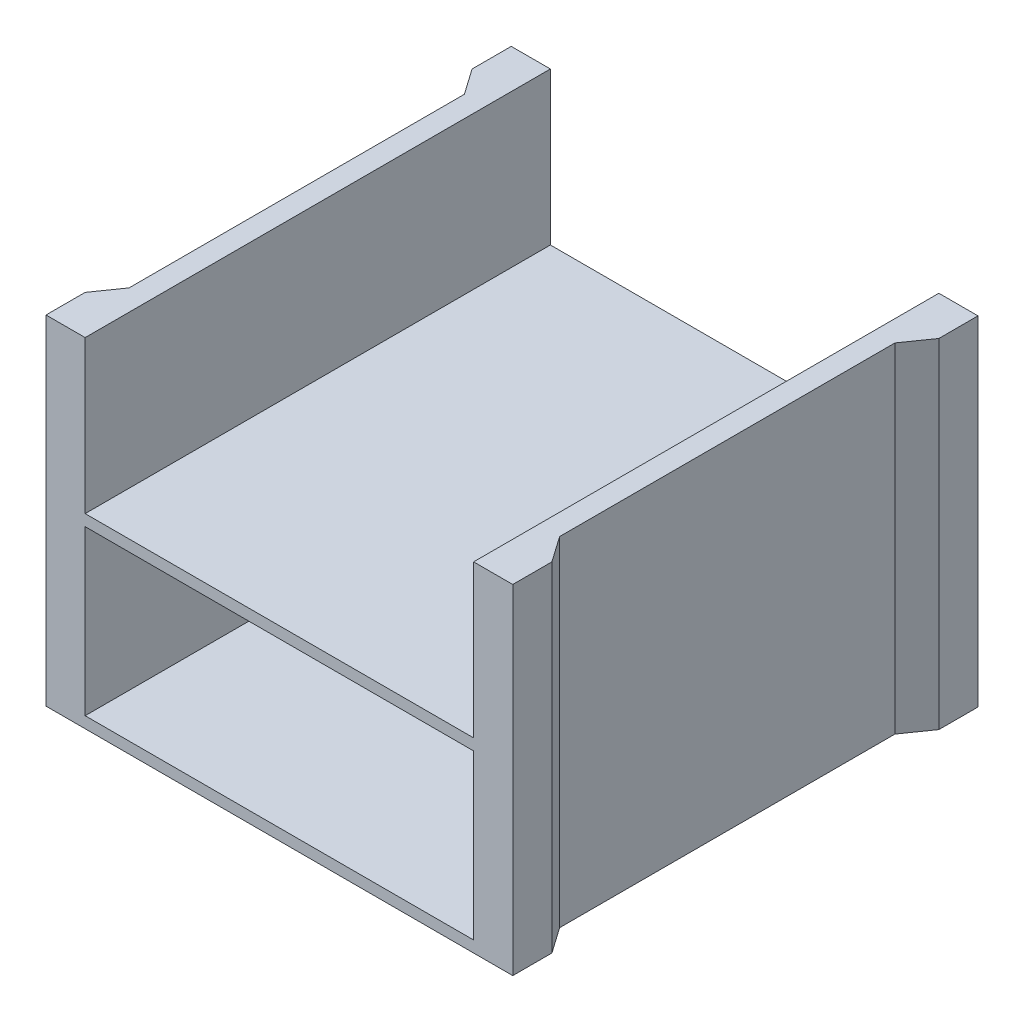
SolidWorks part; units mm, degrees
ref_plane "Front Plane" through (0, 0, 0) normal (0, 0, 1) x (1, 0, 0)
ref_plane "Top Plane" through (0, 0, 0) normal (0, 1, 0) x (1, 0, 0)
ref_plane "Right Plane" through (0, 0, 0) normal (1, 0, 0) x (0, 0, -1)
sketch "Sketch1" plane through (0, 0, 0) normal (0, 1, 0) x (1, 0, 0)
  line L0 (0, 243.586) -> (0, -78.486)
  line L1 (-82.55, -82.55) -> (82.55, -82.55)
  line L2 (-82.55, -82.55) -> (-82.55, 82.55)
  line L3 (-82.55, 82.55) -> (82.55, 82.55)
  line L4 (82.55, -82.55) -> (82.55, 82.55)
  line L5 (-82.55, -82.55) -> (82.55, 82.55) construction
  line L6 (-82.55, 82.55) -> (82.55, -82.55) construction
  line L7 (72.644, 78.486) -> (-72.644, 78.486)
  line L8 (72.644, 78.486) -> (72.644, -78.486)
  line L9 (72.644, -78.486) -> (-72.644, -78.486)
  line L10 (-72.644, 78.486) -> (-72.644, -78.486)
  line L11 (-72.644, 78.486) -> (-78.74, 78.486)
  line L12 (-72.644, 78.486) -> (-72.644, 65.278)
  line L13 (-72.644, 65.278) -> (-78.74, 65.278)
  line L14 (-78.74, 78.486) -> (-78.74, 65.278)
  line L15 (72.644, 0) -> (-72.644, 0)
  line L16 (72.644, 65.278) -> (78.74, 65.278)
  line L17 (78.74, 78.486) -> (78.74, 65.278)
  line L18 (72.644, 78.486) -> (78.74, 78.486)
  line L19 (72.644, 78.486) -> (72.644, 65.278)
  line L20 (72.644, -78.486) -> (78.74, -78.486)
  line L21 (78.74, -78.486) -> (78.74, -65.278)
  line L22 (72.644, -65.278) -> (78.74, -65.278)
  line L23 (72.644, -78.486) -> (72.644, -65.278)
  line L24 (-72.644, -65.278) -> (-78.74, -65.278)
  line L25 (-78.74, -78.486) -> (-78.74, -65.278)
  line L26 (-72.644, -78.486) -> (-78.74, -78.486)
  line L27 (-72.644, -78.486) -> (-72.644, -65.278)
  line L28 (-78.74, 65.278) -> (-72.644, 56.572)
  line L29 (78.74, 65.278) -> (72.644, 56.572)
  line L30 (78.74, -65.278) -> (72.644, -56.572)
  line L31 (-78.74, -65.278) -> (-72.644, -56.572)
  point P0 (0, 0)
  point P26 (0, 82.55)
  dimension "D1" = 165.1
  dimension "D2" = 165.1
  dimension "D3" = 4.064
  dimension "D4" = 4.064
  dimension "D5" = 157.48
  dimension "D6" = 35
  dimension "D7" = 6.096
  dimension "D8" = 13.208
extrude "Boss-Extrude1" add sketch "Sketch1" along normal blind 114.3 contours L15 L8 L7 L0 | L18 L8 L16 L17 | L8 L15 L0 L9 | L0 L15 L10 L9 | L26 L10 L24 L25 | L15 L0 L7 L10 | L12 L13 L14 L11 | L23 L22 L21 L20
sketch "Sketch3" plane through (0, 0, 78.486) normal (0, 0, 1) x (1, 0, 0)
  line L0 (78.74, 114.3) -> (-78.74, 114.3) construction
  line L1 (-65.532, 3.81) -> (65.532, 3.81)
  line L2 (-65.532, 3.81) -> (-65.532, 114.3)
  line L3 (-65.532, 114.3) -> (65.532, 114.3)
  line L4 (65.532, 3.81) -> (65.532, 114.3)
  line L5 (-78.74, 114.3) -> (-78.74, 0) construction
  line L6 (78.74, 114.3) -> (78.74, 0) construction
  line L7 (72.644, 0) -> (-72.644, 0) construction
  line L8 (-65.532, 59.055) -> (65.532, 59.055)
  line L9 (65.532, 59.055) -> (65.532, 62.865)
  line L10 (65.532, 62.865) -> (-65.532, 62.865)
  line L11 (-65.532, 62.865) -> (-65.532, 59.055)
  line M7 (78.74, 114.3) -> (-78.74, 114.3)
  dimension "D1" = 13.208
  dimension "D2" = 13.208
  dimension "D3" = 3.81
  dimension "D4" = 3.81
extrude "Cut-Extrude2" cut sketch "Sketch3" against normal blind 304.8 contours L8 L2 L1 L4 | L10 L4 L2 M7
sketch "Sketch4" plane through (0, 0, 0) normal (0, -1, 0) x (1, 0, 0)
  line L0 (-78.74, 65.278) -> (-72.644, 65.278)
  line L1 (-72.644, 65.278) -> (-72.644, 56.572)
  line L2 (-72.644, 56.572) -> (-78.74, 65.278)
  line L3 (-72.644, -65.278) -> (-78.74, -65.278)
  line L5 (-72.644, -56.572) -> (-72.644, -65.278)
  line L6 (72.644, -65.278) -> (72.644, -56.572)
  line L8 (78.74, -65.278) -> (72.644, -65.278)
  line L9 (72.644, 56.572) -> (72.644, 65.278)
  line L10 (72.644, 65.278) -> (78.74, 65.278)
  line L11 (78.74, 65.278) -> (72.644, 56.572)
  line L12 (-72.644, -56.572) -> (-78.74, -65.278)
  line L13 (78.74, -65.278) -> (72.644, -56.572)
extrude "Boss-Extrude2" add sketch "Sketch4" against normal blind 114.3
